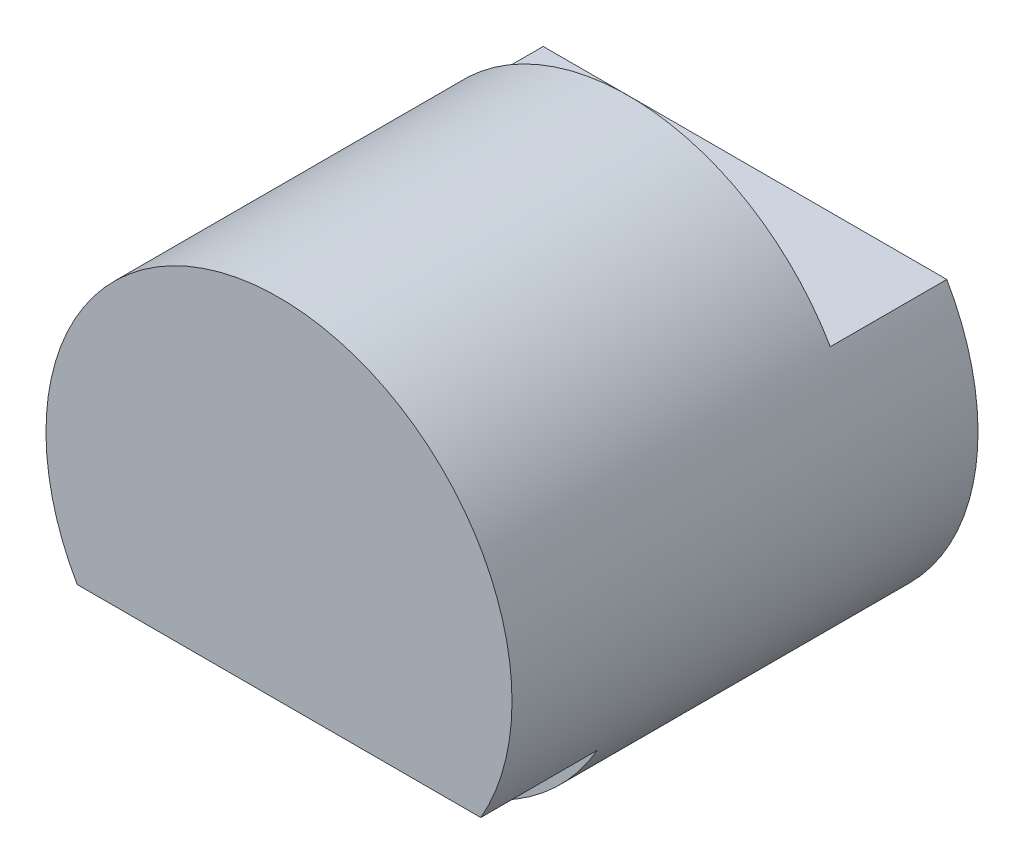
SolidWorks part; units mm, degrees
ref_plane "Front" through (0, 0, 0) normal (0, 0, 1) x (1, 0, 0)
ref_plane "Top" through (0, 0, 0) normal (0, 1, 0) x (1, 0, 0)
ref_plane "Right" through (0, 0, 0) normal (1, 0, 0) x (0, 0, -1)
sketch "Sketch1" plane through (0, 0, 0) normal (0, 0, 1) x (1, 0, 0)
  circle A0 centre (0, 0) radius 2
  dimension "D1" = 4
extrude "Boss-Extrude1" add sketch "Sketch1" along normal blind 3
sketch "Sketch2" plane through (0, 0, 3) normal (0, 0, 1) x (1, 0, 0)
  line L0 (-1.7321, 1) -> (1.7321, 1)
  circle A0 centre (0, 0) radius 2 construction
  arc A1 (-1.7321, 1) -> (1.7321, 1) centre (0, 0) cw
  dimension "D1" = 1
extrude "Boss-Extrude2" add sketch "Sketch2" along normal blind 1
sketch "Sketch3" plane through (0, 0, 0) normal (0, 0, -1) x (-1, 0, 0)
  line L0 (1.7321, 1) -> (-1.7321, 1)
  arc A0 (1.7321, 1) -> (-1.7321, 1) centre (0, 0) ccw
extrude "Cut-Extrude1" cut sketch "Sketch3" against normal blind 1
sketch "Sketch4" plane through (0, 0, 3) normal (0, 0, 1) x (1, 0, 0)
  line L0 (-1.7321, -1) -> (1.7321, -1)
  line L1 (-1.7321, 1) -> (1.7321, 1)
  arc A0 (-1.7321, 1) -> (1.7321, 1) centre (0, 0) ccw construction
  arc A1 (-1.7321, 1) -> (-1.7321, -1) centre (0, 0) ccw
  arc A2 (1.7321, 1) -> (1.7321, -1) centre (0, 0) cw
  dimension "D2" = 2
  dimension "D3" = 2
  dimension "D1" = 1
extrude "Boss-Extrude3" add sketch "Sketch4" along normal blind 1
